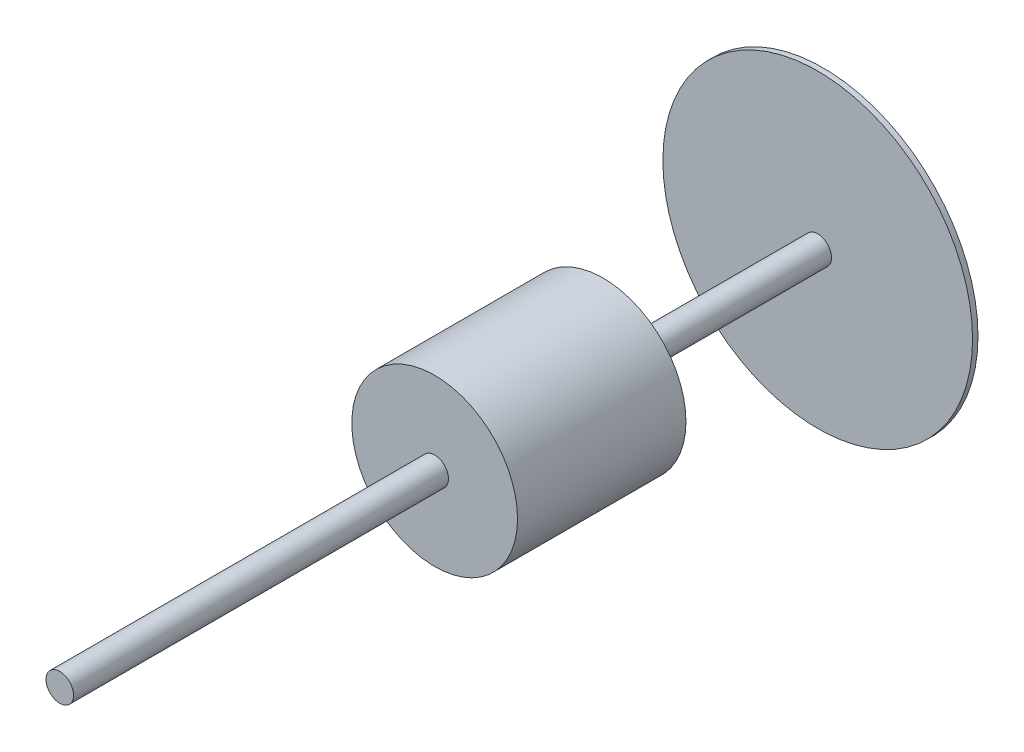
SolidWorks part; units mm, degrees
other "Markup1"
sketch "Sketch6" plane through (500, -500, -1363.6) normal (1, 0, 0) x (0, 0, -1)
ref_plane "Top Plane" through (0, 0, 0) normal (0, 0, 1) x (1, 0, 0)
ref_plane "Right Plane" through (0, 0, 0) normal (0, 1, 0) x (1, 0, 0)
ref_plane "Front Plane" through (0, 0, 0) normal (1, 0, 0) x (0, 0, -1)
sketch "Sketch1" plane through (0, 0, 0) normal (0, 0, 1) x (1, 0, 0)
  circle A0 centre (0, 0) radius 50.8
  dimension "D1" = 101.6
extrude "Boss-Extrude1" add sketch "Sketch1" against normal blind 680 and the other way blind 2130
sketch "Sketch2" plane through (0, 0, -680) normal (0, 0, 1) x (1, 0, 0)
  circle A0 centre (0, 0) radius 570
  dimension "D1" = 1140
extrude "Boss-Extrude2" add sketch "Sketch2" along normal blind 20
sketch "Sketch3" plane through (0, 0, -660) normal (0, 0, 1) x (1, 0, 0)
  circle A0 centre (0, 0) radius 222.25
  dimension "D1" = 444.5
sketch "Sketch7" plane through (0, 0, 2130) normal (0, 0, 1) x (1, 0, 0)
  circle A0 centre (0, 0) radius 305
extrude "Boss-Extrude3" add sketch "Sketch7" along a picked direction on the side against the normal blind 620 from offset 1380 offset against normal yes
sketch "Sketch8" plane through (0, 0, 130) normal (0, 0, -1) x (-1, 0, 0)
  circle A0 centre (0, 0) radius 225
extrude "Boss-Extrude4" add sketch "Sketch8" along normal blind 50
